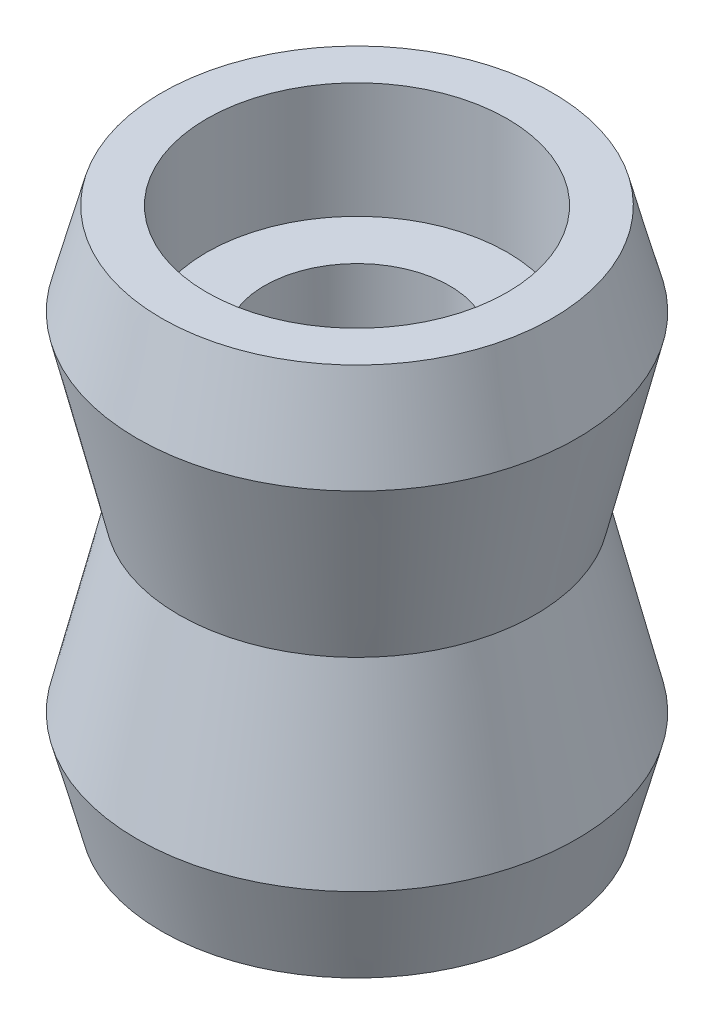
SolidWorks part; units mm, degrees
material "Maple"
ref_plane "Wasteboard" through (0, 0, 0) normal (0, 0, 1) x (1, 0, 0)
ref_plane "Left-Right" through (0, 0, 0) normal (0, 1, 0) x (1, 0, 0)
ref_plane "Front-Back" through (0, 0, 0) normal (1, 0, 0) x (0, 0, -1)
sketch "Sketch1" plane through (0, 0, 0) normal (0, 0, 1) x (1, 0, 0)
  line L0 (0, 42.3235) -> (0, -39.784) construction
  line L1 (0, -55) -> (0, 55) construction
  line L2 (0, 3.1923) -> (40.4814, 3.1923) construction
  line L3 (40.4814, 3.1923) -> (40.4814, 18.1923) construction
  line L4 (30.9163, 3.1923) -> (30.9163, 10.1923) construction
  line L5 (0, 30.7268) -> (2.5, 30.7268) construction
  line L6 (0, 37.5678) -> (4, 37.5678) construction
  line L7 (0, 43.5419) -> (6.5, 43.5419) construction
  line L8 (4, -3.2844) -> (4, 9.669)
  line L9 (4, 9.669) -> (6.5, 9.669)
  line L10 (6.5, 9.669) -> (6.5, 14.669)
  line L11 (6.5, 14.669) -> (8.4483, 14.669)
  line L12 (8.4483, 14.669) -> (9.5, 10.6923)
  line L13 (9.5, 10.6923) -> (7.7, 3.1923)
  line L14 (9.5, -4.3077) -> (7.7, 3.1923)
  line L15 (8.4483, -8.2844) -> (9.5, -4.3077)
  line L16 (6.5, -8.2844) -> (8.4483, -8.2844)
  line L17 (6.5, -3.2844) -> (6.5, -8.2844)
  line L18 (4, -3.2844) -> (6.5, -3.2844)
  line L19 (28.6361, 3.1923) -> (28.6361, 14.6923) construction
  line L20 (28.6361, 14.6923) -> (-15.8373, 14.6923) construction
  line L21 (9.5, 10.6923) -> (7.5155, 18.1962) construction
  point P25 (4, 3.1923)
  dimension "D1" = 15
  dimension "D2" = 7
  dimension "D3" = 4
  dimension "D4" = 2.5
  dimension "D5" = 6.5
  dimension "D6" = 5.5
  dimension "D7" = 7.5
  dimension "D9" = 2.5
  dimension "D10" = 82.1075
  dimension "D11" = 5
  dimension "D13" = 11.5
  dimension "D14" = 3.7
revolve "Revolve1" add sketch "Sketch1" angle 360 about L0
sketch "Sketch2" plane through (0, -3.2844, 0) normal (0, -1, 0) x (1, 0, 0)
  circle A0 centre (0, 0) radius 4
extrude "Boss-Extrude1" add sketch "Sketch2" against normal blind 0.2
